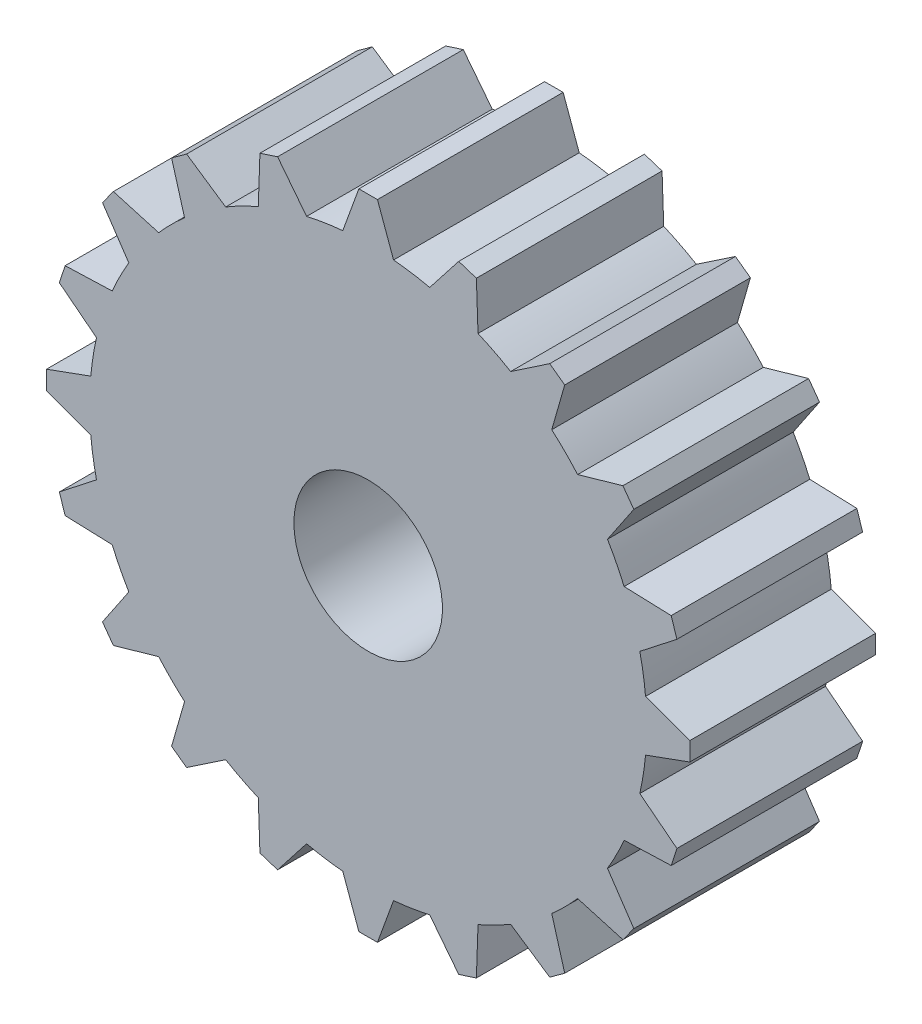
SolidWorks part; units mm, degrees
ref_plane "Ön Düzlem" through (0, 0, 0) normal (0, 0, 1) x (1, 0, 0)
ref_plane "Üst Düzlem" through (0, 0, 0) normal (0, 1, 0) x (1, 0, 0)
ref_plane "Sağ Düzlem" through (0, 0, 0) normal (1, 0, 0) x (0, 0, -1)
sketch "Çizim1" plane through (0, 0, 0) normal (0, 0, 1) x (1, 0, 0)
  circle A0 centre (0, 0) radius 15
  dimension "D1" = 30
extrude "Yükseklik-Ekstrüzyon1" add sketch "Çizim1" along normal mid plane 10
ref_plane "Düzlem1" through (0, 0, 5) normal (0, 0, 1) x (1, 0, 0)
sketch "Çizim2" plane through (0, 0, 0) normal (0, 0, 1) x (1, 0, 0)
  line L0 (0, 0) -> (0, 15) construction
  line L1 (-2, 13.2) -> (2, 13.2)
  line L2 (2, 13.2) -> (0.5, 17.3212)
  line L3 (0.5, 17.3212) -> (-0.5, 17.3212)
  line L4 (-0.5, 17.3212) -> (-2, 13.2)
  line L5 (4.877, 16.628) -> (2.1769, 13.172)
  line L6 (5.8281, 16.3189) -> (4.877, 16.628)
  line L7 (5.9811, 11.9359) -> (5.8281, 16.3189)
  line L8 (2.1769, 13.172) -> (5.9811, 11.9359)
  line L9 (9.7766, 14.3071) -> (6.1407, 11.8546)
  line L10 (10.5857, 13.7193) -> (9.7766, 14.3071)
  line L11 (9.3768, 9.5035) -> (10.5857, 13.7193)
  line L12 (6.1407, 11.8546) -> (9.3768, 9.5035)
  line L13 (13.7193, 10.5857) -> (9.5035, 9.3768)
  line L14 (14.3071, 9.7766) -> (13.7193, 10.5857)
  line L15 (11.8546, 6.1407) -> (14.3071, 9.7766)
  line L16 (9.5035, 9.3768) -> (11.8546, 6.1407)
  line L17 (16.3189, 5.8281) -> (11.9359, 5.9811)
  line L18 (16.628, 4.877) -> (16.3189, 5.8281)
  line L19 (13.172, 2.1769) -> (16.628, 4.877)
  line L20 (11.9359, 5.9811) -> (13.172, 2.1769)
  line L21 (17.3212, 0.5) -> (13.2, 2)
  line L22 (17.3212, -0.5) -> (17.3212, 0.5)
  line L23 (13.2, -2) -> (17.3212, -0.5)
  line L24 (13.2, 2) -> (13.2, -2)
  line L25 (16.628, -4.877) -> (13.172, -2.1769)
  line L26 (16.3189, -5.8281) -> (16.628, -4.877)
  line L27 (11.9359, -5.9811) -> (16.3189, -5.8281)
  line L28 (13.172, -2.1769) -> (11.9359, -5.9811)
  line L29 (14.3071, -9.7766) -> (11.8546, -6.1407)
  line L30 (13.7193, -10.5857) -> (14.3071, -9.7766)
  line L31 (9.5035, -9.3768) -> (13.7193, -10.5857)
  line L32 (11.8546, -6.1407) -> (9.5035, -9.3768)
  line L33 (10.5857, -13.7193) -> (9.3768, -9.5035)
  line L34 (9.7766, -14.3071) -> (10.5857, -13.7193)
  line L35 (6.1407, -11.8546) -> (9.7766, -14.3071)
  line L36 (9.3768, -9.5035) -> (6.1407, -11.8546)
  line L37 (5.8281, -16.3189) -> (5.9811, -11.9359)
  line L38 (4.877, -16.628) -> (5.8281, -16.3189)
  line L39 (2.1769, -13.172) -> (4.877, -16.628)
  line L40 (5.9811, -11.9359) -> (2.1769, -13.172)
  line L41 (0.5, -17.3212) -> (2, -13.2)
  line L42 (-0.5, -17.3212) -> (0.5, -17.3212)
  line L43 (-2, -13.2) -> (-0.5, -17.3212)
  line L44 (2, -13.2) -> (-2, -13.2)
  line L45 (-4.877, -16.628) -> (-2.1769, -13.172)
  line L46 (-5.8281, -16.3189) -> (-4.877, -16.628)
  line L47 (-5.9811, -11.9359) -> (-5.8281, -16.3189)
  line L48 (-2.1769, -13.172) -> (-5.9811, -11.9359)
  line L49 (-9.7766, -14.3071) -> (-6.1407, -11.8546)
  line L50 (-10.5857, -13.7193) -> (-9.7766, -14.3071)
  line L51 (-9.3768, -9.5035) -> (-10.5857, -13.7193)
  line L52 (-6.1407, -11.8546) -> (-9.3768, -9.5035)
  line L53 (-13.7193, -10.5857) -> (-9.5035, -9.3768)
  line L54 (-14.3071, -9.7766) -> (-13.7193, -10.5857)
  line L55 (-11.8546, -6.1407) -> (-14.3071, -9.7766)
  line L56 (-9.5035, -9.3768) -> (-11.8546, -6.1407)
  line L57 (-16.3189, -5.8281) -> (-11.9359, -5.9811)
  line L58 (-16.628, -4.877) -> (-16.3189, -5.8281)
  line L59 (-13.172, -2.1769) -> (-16.628, -4.877)
  line L60 (-11.9359, -5.9811) -> (-13.172, -2.1769)
  line L61 (-17.3212, -0.5) -> (-13.2, -2)
  line L62 (-17.3212, 0.5) -> (-17.3212, -0.5)
  line L63 (-13.2, 2) -> (-17.3212, 0.5)
  line L64 (-13.2, -2) -> (-13.2, 2)
  line L65 (-16.628, 4.877) -> (-13.172, 2.1769)
  line L66 (-16.3189, 5.8281) -> (-16.628, 4.877)
  line L67 (-11.9359, 5.9811) -> (-16.3189, 5.8281)
  line L68 (-13.172, 2.1769) -> (-11.9359, 5.9811)
  line L69 (-14.3071, 9.7766) -> (-11.8546, 6.1407)
  line L70 (-13.7193, 10.5857) -> (-14.3071, 9.7766)
  line L71 (-9.5035, 9.3768) -> (-13.7193, 10.5857)
  line L72 (-11.8546, 6.1407) -> (-9.5035, 9.3768)
  line L73 (-10.5857, 13.7193) -> (-9.3768, 9.5035)
  line L74 (-9.7766, 14.3071) -> (-10.5857, 13.7193)
  line L75 (-6.1407, 11.8546) -> (-9.7766, 14.3071)
  line L76 (-9.3768, 9.5035) -> (-6.1407, 11.8546)
  line L77 (-5.8281, 16.3189) -> (-5.9811, 11.9359)
  line L78 (-4.877, 16.628) -> (-5.8281, 16.3189)
  line L79 (-2.1769, 13.172) -> (-4.877, 16.628)
  line L80 (-5.9811, 11.9359) -> (-2.1769, 13.172)
  circle A0 centre (0, 0) radius 15 construction
  circle A1 centre (0, 0) radius 15 construction
  point P90 (0, 0)
  dimension "D7" = 20
  dimension "D1" = 2
  dimension "D2" = 2
  dimension "D3" = 70
  dimension "D4" = 70
  dimension "D5" = 1
  dimension "D6" = 13.2
  dimension "D8" = 13.3507
  dimension "D9" = 13.2
extrude "Yükseklik-Ekstrüzyon2" add sketch "Çizim2" along normal mid plane 10
sketch "Çizim3" plane through (0, 0, -5) normal (0, 0, -1) x (-1, 0, 0)
  circle A0 centre (0, 0) radius 4
  dimension "D1" = 8
extrude "Kes-Ekstrüzyon1" cut sketch "Çizim3" against normal through all
